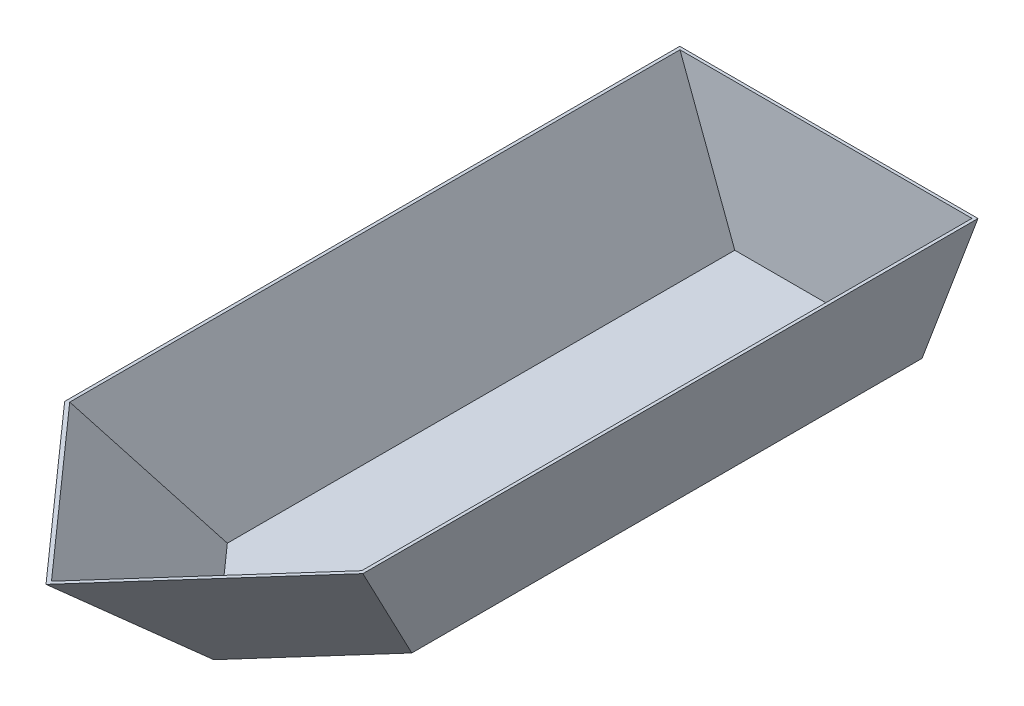
SolidWorks part; units mm, degrees
ref_plane "Front Plane" through (0, 0, 0) normal (0, 0, 1) x (1, 0, 0)
ref_plane "Top Plane" through (0, 0, 0) normal (0, 1, 0) x (1, 0, 0)
ref_plane "Right Plane" through (0, 0, 0) normal (1, 0, 0) x (0, 0, -1)
sketch "Sketch1" plane through (0, 0, 0) normal (0, 0, 1) x (1, 0, 0)
  line L0 (0, 0) -> (508, 0)
  line L1 (0, 0) -> (0, 406.4) construction
  line L2 (0, 406.4) -> (-152.4, 406.4) construction
  line L3 (-152.4, 406.4) -> (0, 0)
  line L4 (508, 0) -> (660.4, 0) construction
  line L5 (508, 0) -> (660.4, 406.4)
  line L6 (660.4, 406.4) -> (-152.4, 406.4)
  line L7 (660.4, 0) -> (660.4, 406.4) construction
  dimension "D1" = 508
  dimension "D2" = 406.4
  dimension "D3" = 152.4
  dimension "D4" = 152.4
extrude "Boss-Extrude1" add sketch "Sketch1" along normal blind 2133.6
sketch "Sketch4" plane through (0, 406.4, 0) normal (0, 1, 0) x (1, 0, 0)
  line L4 (660.4, -2133.6) -> (660.4, -1676.4) construction
  line L5 (660.4, -2133.6) -> (660.4, 0) construction
  line L6 (660.4, -1676.4) -> (-152.4, -1676.4) construction
  line L7 (-152.4, -2133.6) -> (-152.4, 0) construction
  line L11 (-152.4, -1676.4) -> (254, -2133.6) construction
  line L12 (660.4, -2133.6) -> (-152.4, -2133.6) construction
  line L13 (254, -2133.6) -> (660.4, -1676.4) construction
  dimension "D1" = 457.2
ref_plane "Plane2" through (254, 0, 0) normal (1, 0, 0) x (0, 0, -1)
sketch "Sketch13" plane through (254, 0, 0) normal (1, 0, 0) x (0, 0, -1)
  line L0 (-2133.6, 0) -> (-3174.6486, 0)
  line L1 (-2133.6, 406.4) -> (-1676.4, 0)
  line L2 (-2133.6, 406.4) -> (-1676.4, 406.4) construction
  line L3 (-2133.6, 0) -> (0, 0) construction
  line L5 (-2133.6, 0) -> (-1676.4, 0)
  line L6 (-3174.6486, 0) -> (-3174.6486, 406.4)
  line L7 (-3174.6486, 406.4) -> (-2133.6, 406.4)
  dimension "D1" = 457.2
extrude "Cut-Extrude2" cut sketch "Sketch13" along direction (0.6644, 0, 0.7474) on the side against the normal through all and the other way through all contours L7 L1 L5 L0 L6
mirror "Mirror1" about plane through (254, 0, 0) normal (1, 0, 0) of "Cut-Extrude2"
shell "Shell1" thickness 7.9375
ref_plane "Plane3" through (0, 0, 1671.0211) normal (0, 0, -1) x (-1, 0, 0)
sketch "Sketch17" plane through (0, 0, 1671.0211) normal (0, 0, -1) x (-1, 0, 0)
  line L0 (-660.4, 406.4) -> (-580.4525, 597.9254)
  line L1 (-580.4525, 597.9254) -> (23.2662, 597.9254)
  line L2 (23.2662, 597.9254) -> (152.4, 406.4)
  line L3 (-660.4, 406.4) -> (152.4, 406.4)
